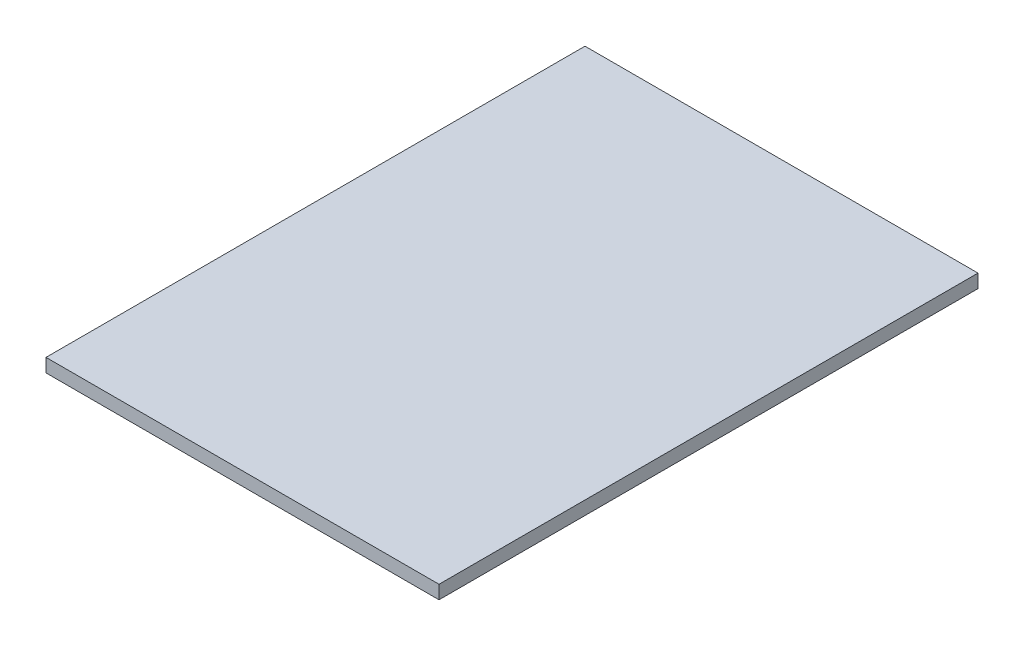
SolidWorks part; units mm, degrees
ref_plane "Front Plane" through (0, 0, 0) normal (0, 0, 1) x (1, 0, 0)
ref_plane "Top Plane" through (0, 0, 0) normal (0, 1, 0) x (1, 0, 0)
ref_plane "Right Plane" through (0, 0, 0) normal (1, 0, 0) x (0, 0, -1)
sketch "Sketch1" plane through (0, 0, 0) normal (0, 1, 0) x (1, 0, 0)
  line L1 (-137.6667, 238) -> (212.3333, 238)
  line L2 (-137.6667, 238) -> (-137.6667, -242)
  line L3 (-137.6667, -242) -> (212.3333, -242)
  line L4 (212.3333, 238) -> (212.3333, -242)
  dimension "D1" = 350
  dimension "D2" = 480
extrude "Boss-Extrude1" add sketch "Sketch1" along normal blind 12
